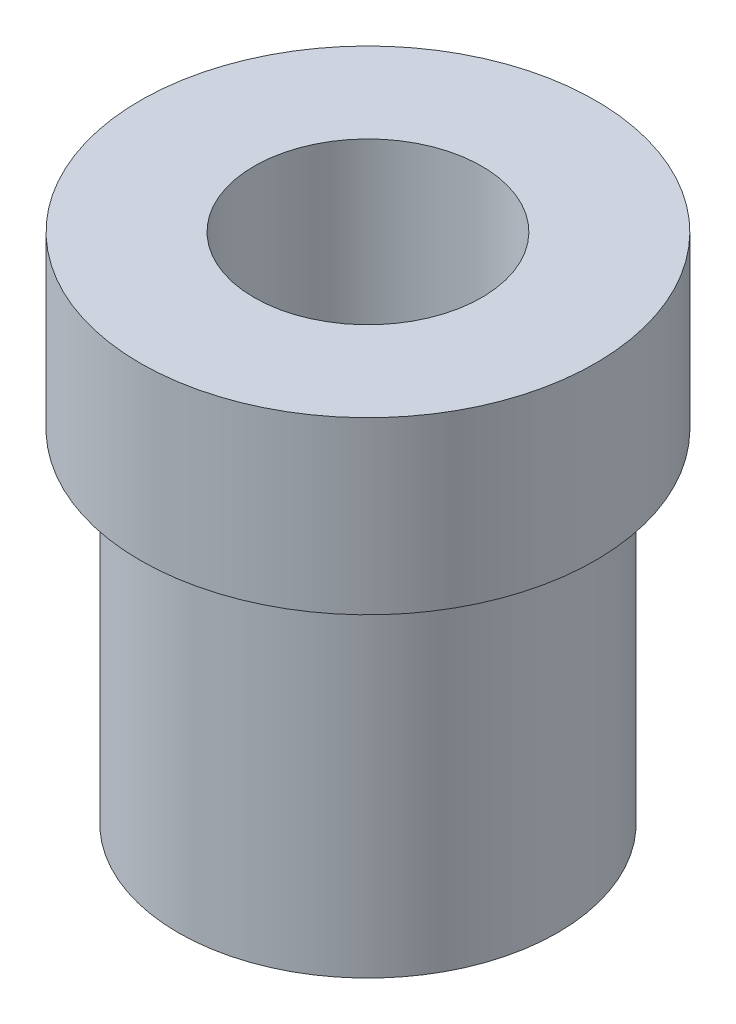
SolidWorks part; units mm, degrees
ref_plane "Front Plane" through (0, 0, 0) normal (0, 0, 1) x (1, 0, 0)
ref_plane "Top Plane" through (0, 0, 0) normal (0, 1, 0) x (1, 0, 0)
ref_plane "Right Plane" through (0, 0, 0) normal (1, 0, 0) x (0, 0, -1)
sketch "Sketch1" plane through (0, 0, 0) normal (0, 1, 0) x (1, 0, 0)
  circle A0 centre (0, 0) radius 5
  dimension "D1" = 10
extrude "Boss-Extrude1" add sketch "Sketch1" along normal blind 9
sketch "Sketch2" plane through (0, 9, 0) normal (0, 1, 0) x (1, 0, 0)
  circle A0 centre (0, 0) radius 6
  dimension "D1" = 12
extrude "Boss-Extrude2" add sketch "Sketch2" along normal blind 4.5
sketch "Sketch3" plane through (0, 13.5, 0) normal (0, 1, 0) x (1, 0, 0)
  circle A0 centre (0, 0) radius 3
  dimension "D1" = 6
extrude "Cut-Extrude1" cut sketch "Sketch3" against normal through all both and the other way through all
